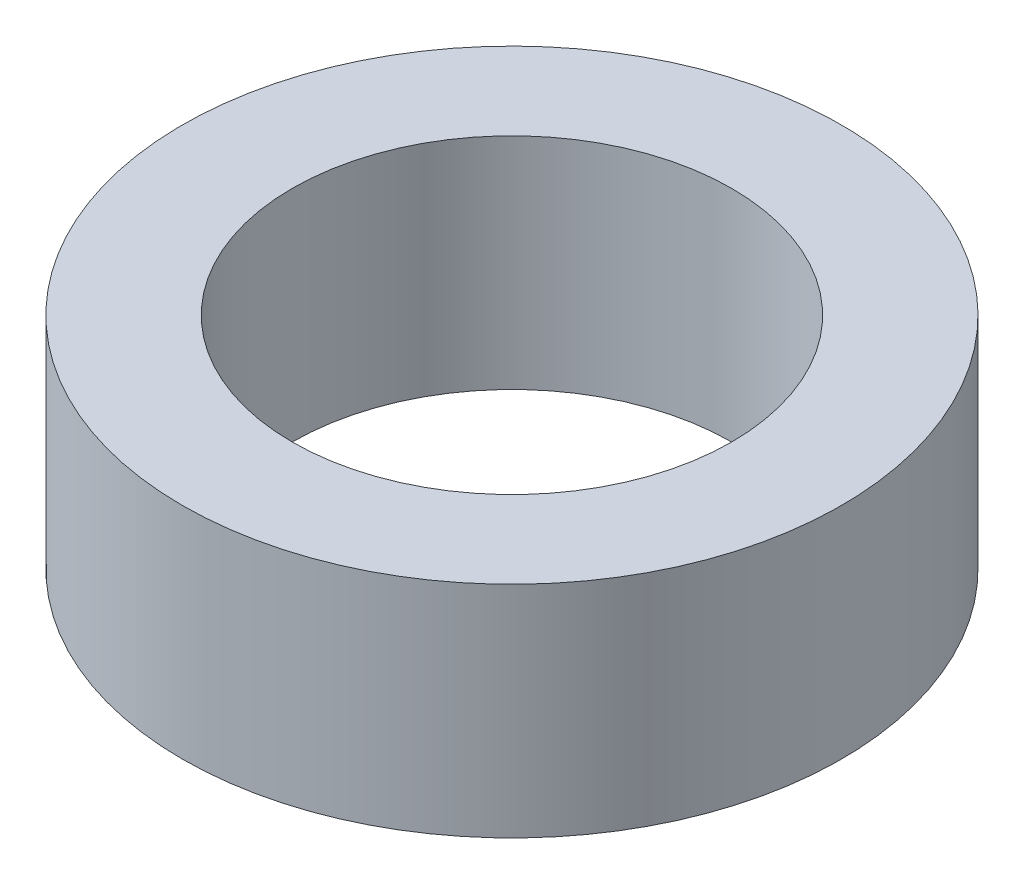
SolidWorks part; units mm, degrees
ref_plane "Front Plane" through (0, 0, 0) normal (0, 0, 1) x (1, 0, 0)
ref_plane "Top Plane" through (0, 0, 0) normal (0, 1, 0) x (1, 0, 0)
ref_plane "Right Plane" through (0, 0, 0) normal (1, 0, 0) x (0, 0, -1)
sketch "Sketch1" plane through (0, 0, 0) normal (0, 1, 0) x (1, 0, 0)
  circle A0 centre (0, 0) radius 3
  circle A1 centre (0, 0) radius 2
  dimension "D2" = 6
  dimension "D1" = 1
extrude "Boss-Extrude1" add sketch "Sketch1" along normal blind 2
